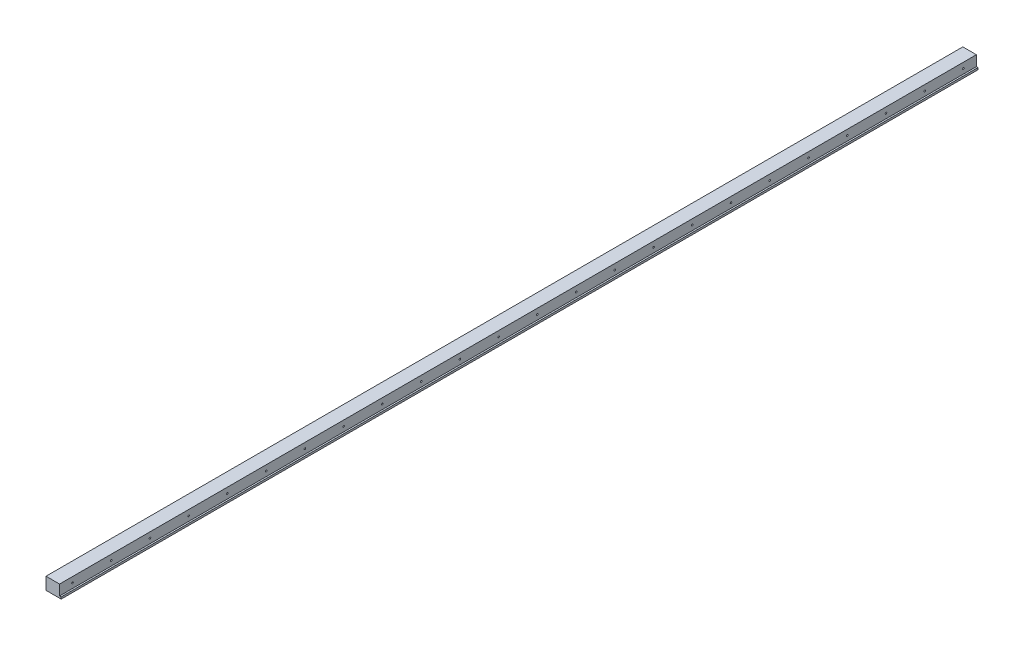
SolidWorks part; units mm, degrees
ref_plane "Front" through (0, 0, 0) normal (0, 0, 1) x (1, 0, 0)
ref_plane "Top" through (0, 0, 0) normal (0, 1, 0) x (1, 0, 0)
ref_plane "Right" through (0, 0, 0) normal (1, 0, 0) x (0, 0, -1)
sketch "Sketch1" plane through (0, 0, 0) normal (1, 0, 0) x (0, 0, -1)
  line L1 (0, 0) -> (1420, 0)
  line L2 (0, 0) -> (0, 19)
  line L3 (0, 19) -> (1420, 19)
  line L4 (1420, 0) -> (1420, 19)
  dimension "D1" = 1420
  dimension "D2" = 19
extrude "Boss-Extrude1" add sketch "Sketch1" along normal blind 23.5
sketch "Sketch2" plane through (23.5, 0, 0) normal (-1, 0, 0) x (0, 0, 1)
  line L0 (-1420, 0) -> (-1420, 19) construction
  line L1 (0, 19) -> (-1420, 19)
  line L2 (0, 19) -> (0, 3)
  line L3 (0, 3) -> (-1420, 3)
  line L4 (-1420, 19) -> (-1420, 3)
  dimension "D1" = 3
extrude "Cut-Extrude1" cut sketch "Sketch2" along normal blind 2.5
hole_wizard "M4x0.7 Tapped Hole1" positions "Sketch4" profile "Sketch3" tap size "M4x0.7" standard "JIS"
sketch "Sketch4" plane through (0, -2.4958, -42.1442) normal (1, 0, 0) x (0, 0, -1)
  line L0 (-42.1442, 21.4958) -> (-42.1442, 2.4958) construction
  point P0 (-14.1442, 12.9958)
  dimension "D1" = 10.5
  dimension "D2" = 28
sketch "Sketch3" plane through (0, 10.5, -28) normal (0, 1, 0) x (0, 0, 1)
  line L0 (0, 0) -> (0, 11.5914)
  line L1 (0, 11.5914) -> (1.65, 10.6)
  line L2 (1.65, 10.6) -> (1.65, 0)
  line L5 (1.65, 0) -> (0, 0)
  line L10 (0, 11.5914) -> (-1.65, 10.6) construction
  line L11 (0, -6.35) -> (0, 107.95) construction
  dimension "Tap Drill Dia." = 3.3
  dimension "Tap Drill Depth" = 10.6
  dimension "Drill Angle" = 118
cosmetic thread "Hole Thread2" parameters "D1"=8.5, "D2"=4
pattern_linear "LPattern1" count 24 spacing 60 along (0, 0, -1) of "M4x0.7 Tapped Hole1"
hole_wizard "M3x0.5 Tapped Hole1" positions "Sketch6" profile "Sketch5" tap size "M3x0.5" standard "JIS"
sketch "Sketch6" plane through (21, 0, 0) normal (1, 0, 0) x (0, 0, -1)
  point P0 (20, 10.5)
  dimension "D1" = 10.5
  dimension "D2" = 20
sketch "Sketch5" plane through (21, 10.5, -20) normal (0, 1, 0) x (0, 0, -1)
  line L0 (0, 0) -> (0, 10.7511)
  line L1 (0, 10.7511) -> (1.25, 10)
  line L2 (1.25, 10) -> (1.25, 0)
  line L5 (1.25, 0) -> (0, 0)
  line L10 (0, 10.7511) -> (-1.25, 10) construction
  line L11 (0, -6.35) -> (0, 107.95) construction
  dimension "Tap Drill Dia." = 2.5
  dimension "Tap Drill Depth" = 10
  dimension "Drill Angle" = 118
cosmetic thread "Hole Thread1" parameters "D1"=8.5, "D2"=3
pattern_linear "LPattern2" count 24 spacing 60 along (0, 0, -1) of "M3x0.5 Tapped Hole1"
